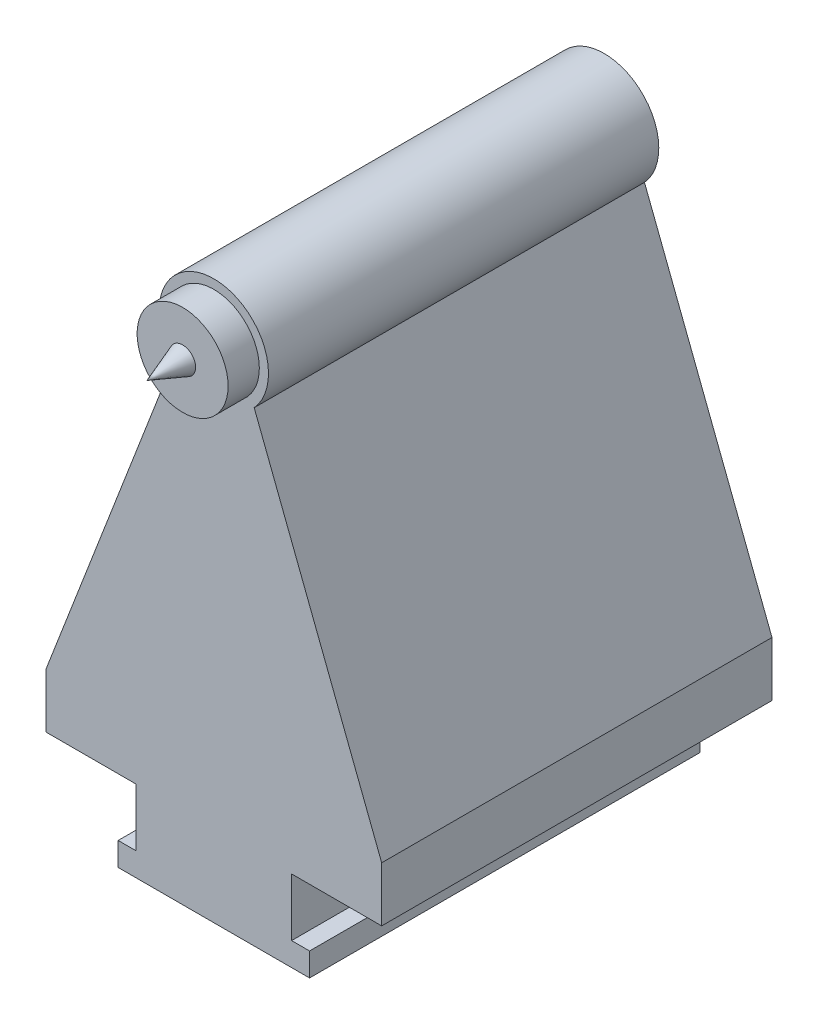
SolidWorks part; units mm, degrees
ref_plane "Płaszczyzna przednia" through (0, 0, 0) normal (0, 0, 1) x (1, 0, 0)
ref_plane "Płaszczyzna górna" through (0, 0, 0) normal (0, 1, 0) x (1, 0, 0)
ref_plane "Płaszczyzna prawa" through (0, 0, 0) normal (1, 0, 0) x (0, 0, -1)
sketch "Szkic1" plane through (0, 0, 0) normal (0, 0, 1) x (1, 0, 0)
  line L5 (12.5, 144) -> (70.2, 144)
  line L6 (70.2, 144) -> (70.2, 107)
  line L7 (70.2, 107) -> (58.7, 107)
  line L8 (58.7, 107) -> (58.7, 92)
  line L10 (181.3, 92) -> (181.3, 107)
  line L11 (181.3, 107) -> (169.8, 107)
  line L12 (169.8, 107) -> (169.8, 144)
  line L13 (169.8, 144) -> (227.5, 144)
  line L17 (58.7, 92) -> (181.3, 92)
  line L18 (12.5, 144) -> (12.5, 179)
  line L19 (227.5, 144) -> (227.5, 179)
  line L20 (227.5, 179) -> (145.8329, 390.6151)
  line L24 (94.1671, 390.6151) -> (12.5, 179)
  circle A0 centre (120, 414.23) radius 35
  dimension "D10" = 270.23
  dimension "D2" = 215
  dimension "D3" = 11.5
  dimension "D4" = 37
  dimension "D5" = 122.6
  dimension "D6" = 11.5
  dimension "D7" = 15
  dimension "D8" = 15
  dimension "D9" = 35
  dimension "D12" = 37
extrude "Dodanie-wyciągnięcie2" add sketch "Szkic1" along normal blind 250 contours A0 L24 L18 L5 L6 L7 L8 L17 L10 L11 L12 L13 L19 L20 | A0
sketch "Szkic4" plane through (0, 0, 250) normal (0, 0, 1) x (1, 0, 0)
  circle A0 centre (120, 414.23) radius 29.1296
extrude "Dodanie-wyciągnięcie3" add sketch "Szkic4" along normal blind 20
sketch "Szkic5" plane through (0, 0, 270) normal (0, 0, 1) x (1, 0, 0)
  circle A0 centre (120, 414.23) radius 8.316
extrude "Dodanie-wyciągnięcie4" add sketch "Szkic5" along normal blind 36 draft 20
